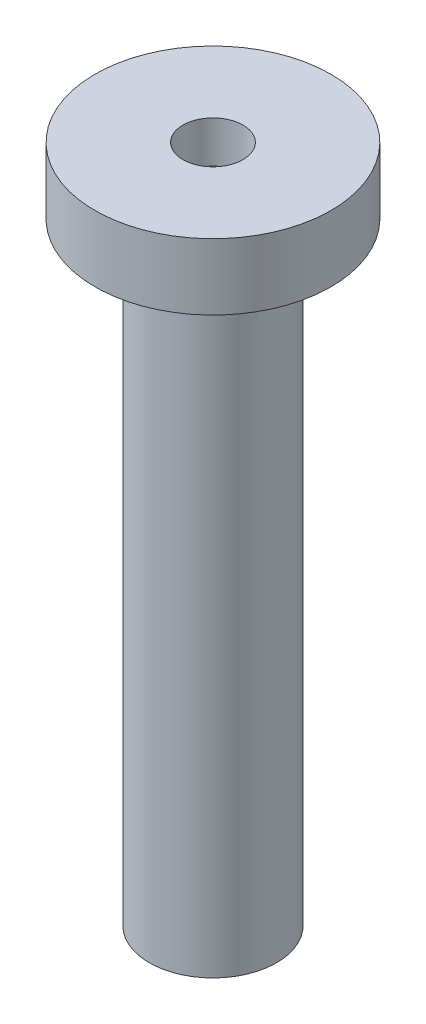
SolidWorks part; units mm, degrees
ref_plane "Front Plane" through (0, 0, 0) normal (0, 0, 1) x (1, 0, 0)
ref_plane "Top Plane" through (0, 0, 0) normal (0, 1, 0) x (1, 0, 0)
ref_plane "Right Plane" through (0, 0, 0) normal (1, 0, 0) x (0, 0, -1)
sketch "Sketch2" plane through (0, 0, 0) normal (0, 0, 1) x (1, 0, 0)
  line L0 (0, 0) -> (0, 22.5126) construction
  line L1 (0, 0) -> (1.3, 0)
  line L2 (1.3, 0) -> (1.3, 12.5)
  line L3 (1.3, 12.5) -> (2.4086, 12.5)
  line L4 (2.4086, 12.5) -> (2.4086, 13.85)
  line L5 (2.4086, 13.85) -> (0.6122, 13.85)
  line L6 (0.6122, 13.85) -> (0.6122, 12.9976)
  line L7 (0.6122, 12.9976) -> (0, 12.5)
  line L8 (0, 0) -> (0, 12.5)
  point P5 (1.2201, 13.2681)
  point P11 (0, 12.5)
  point P12 (0.6122, 12.9976)
  dimension "D1" = 12.5
  dimension "D2" = 2.6
revolve "Revolve1" add sketch "Sketch2" angle 360 about L0
